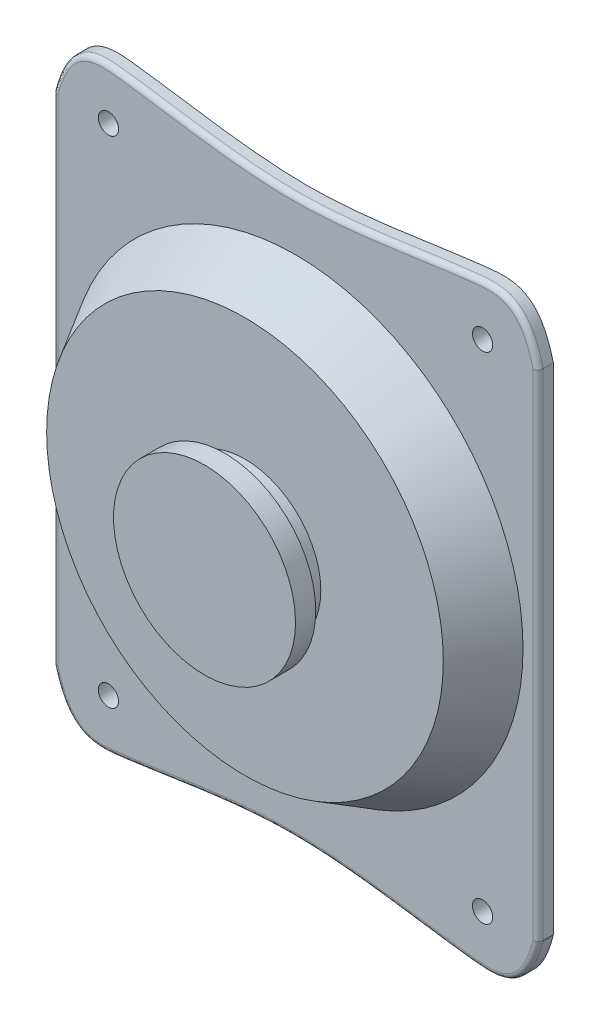
SolidWorks part; units mm, degrees
ref_plane "Front Plane" through (0, 0, 0) normal (0, 0, 1) x (1, 0, 0)
ref_plane "Top Plane" through (0, 0, 0) normal (0, 1, 0) x (1, 0, 0)
ref_plane "Right Plane" through (0, 0, 0) normal (1, 0, 0) x (0, 0, -1)
sketch "Sketch1" plane through (0, 0, 0) normal (0, 0, 1) x (1, 0, 0)
  line L2 (-24, 24.5) -> (-24, -24.5)
  line L4 (24, 24.5) -> (24, -24.5)
  line L5 (-24, 0) -> (24, 0) construction
  spline S0 degree 3 poles (-24, -24.5) (-22.6056, -29.9523) (-14.1064, -29.1494) (-0.2309, -26.3219) (15.046, -29.3894) (22.6642, -29.8454) (24, -24.5) knots 0 0 0 0 0.159887 0.492954 0.826022 1 1 1 1
  spline S1 degree 3 poles (-24, 24.5) (-22.6056, 29.9523) (-14.1064, 29.1494) (-0.2309, 26.3219) (15.046, 29.3894) (22.6642, 29.8454) (24, 24.5) knots 0 0 0 0 0.159887 0.492954 0.826022 1 1 1 1
  point P4 (-19, -29.4992)
  point P5 (19, -29.4992)
  point P6 (-24, -24.5)
  point P7 (24, -24.5)
  point P8 (0, -27.5)
extrude "Boss-Extrude1" add sketch "Sketch1" along normal blind 1.5
sketch "Sketch2" plane through (0, 0, 1.5) normal (0, 0, 1) x (1, 0, 0)
  circle A0 centre (0, 0) radius 22.5
extrude "Boss-Extrude4" add sketch "Sketch2" along normal blind 5 draft 30
sketch "Sketch3" plane through (0, 0, 6.5) normal (0, 0, 1) x (1, 0, 0)
  circle A0 centre (0, 0) radius 7.5
extrude "Boss-Extrude5" add sketch "Sketch3" along normal blind 2
sketch "Sketch4" plane through (0, 0, 8.5) normal (0, 0, 1) x (1, 0, 0)
  circle A0 centre (0, 0) radius 9
extrude "Boss-Extrude7" add sketch "Sketch4" along normal blind 2
fillet "Fillet4" radius 0.5 4 edges at (-24, 0, 1.5) (24, 0, 1.5)
sketch "Sketch5" plane through (0, 0, 1.5) normal (0, 0, 1) x (1, 0, 0)
  line L0 (23.5, -24.438) -> (23.5, 24.438) construction
  line L1 (0, 27) -> (0, -27) construction
  line L2 (-23.5, 0) -> (23.5, 0) construction
  line L3 (-23.5, 24.4366) -> (-23.5, -24.4366) construction
  circle A0 centre (18.5, -24.5) radius 1
  circle A1 centre (-18.5, -24.5) radius 1
  circle A2 centre (18.5, 24.5) radius 1
  circle A3 centre (-18.5, 24.5) radius 1
  spline S0 degree 3 poles (23.5, 24.438) (23.3649, 24.9705) (23.2056, 25.4945) (22.8028, 26.5126) (22.5583, 27.0108) (22.0826, 27.6811) (21.903, 27.8939) (21.5044, 28.2683) (21.2827, 28.4322) (20.7982, 28.6965) (20.543, 28.7933) (20.0115, 28.9289) (19.7368, 28.9672) (18.9221, 29.0217) (18.3788, 28.9835) (17.2921, 28.8747) (16.7499, 28.8076) (15.1245, 28.6027) (14.043, 28.4508) (10.7993, 27.9884) (8.637, 27.6712) (4.2973, 27.1834) (2.1216, 27.0105) (-2.2508, 26.9887) (-4.4207, 27.142) (-8.7434, 27.6174) (-10.8963, 27.9392) (-14.1261, 28.4176) (-15.2028, 28.5762) (-16.5506, 28.7599) (-16.8203, 28.7959) (-17.3599, 28.866) (-17.6299, 28.9007) (-18.1706, 28.9586) (-18.4412, 28.9819) (-18.9837, 29.0036) (-19.2568, 29.0021) (-19.7997, 28.9565) (-20.0668, 28.9127) (-20.5885, 28.7645) (-20.8441, 28.658) (-21.3097, 28.3875) (-21.5243, 28.2225) (-21.9177, 27.8423) (-22.0901, 27.6343) (-22.4012, 27.1929) (-22.5403, 26.9586) (-22.7907, 26.4761) (-22.9015, 26.2295) (-23.2031, 25.478) (-23.3636, 24.9618) (-23.5, 24.4366) knots 0 0 0 0 0.03125 0.03125 0.0625 0.0625 0.078125 0.078125 0.09375 0.09375 0.109375 0.109375 0.125 0.125 0.15625 0.15625 0.1875 0.1875 0.25 0.25 0.375 0.375 0.5 0.5 0.625 0.625 0.75 0.75 0.8125 0.8125 0.828125 0.828125 0.84375 0.84375 0.859375 0.859375 0.875 0.875 0.890625 0.890625 0.90625 0.90625 0.921875 0.921875 0.9375 0.9375 0.953125 0.953125 0.96875 0.96875 1 1 1 1 construction
  spline S1 degree 3 poles (-23.5, -24.4366) (-23.3635, -24.9622) (-23.2031, -25.4775) (-22.8033, -26.4746) (-22.5662, -26.9573) (-22.0929, -27.6312) (-21.9175, -27.8424) (-21.5256, -28.2213) (-21.3043, -28.3916) (-20.833, -28.6635) (-20.582, -28.7672) (-20.0521, -28.916) (-19.7817, -28.959) (-18.9686, -29.0244) (-18.4182, -28.9859) (-17.6038, -28.8976) (-17.3331, -28.8626) (-16.7917, -28.7921) (-15.4389, -28.6112) (-14.0885, -28.412) (-10.8478, -27.932) (-8.6874, -27.6096) (-4.3512, -27.136) (-2.1751, -26.9852) (2.2068, -27.015) (4.3805, -27.1911) (8.7129, -27.6816) (10.8715, -27.9989) (14.1108, -28.4604) (15.1908, -28.6117) (16.8134, -28.8153) (17.3543, -28.8824) (18.4393, -28.988) (18.9853, -29.0232) (19.7985, -28.9597) (20.071, -28.9176) (20.5941, -28.7755) (20.8478, -28.6742) (21.3237, -28.4041) (21.5387, -28.2401) (21.9303, -27.8636) (22.1059, -27.6513) (22.4159, -27.2081) (22.5525, -26.9749) (22.7998, -26.4918) (22.9103, -26.2419) (23.2086, -25.4844) (23.3662, -24.9653) (23.5, -24.438) knots 0 0 0 0 0.03125 0.03125 0.0625 0.0625 0.078125 0.078125 0.09375 0.09375 0.109375 0.109375 0.125 0.125 0.15625 0.15625 0.171875 0.171875 0.1875 0.25 0.25 0.375 0.375 0.5 0.5 0.625 0.625 0.75 0.75 0.8125 0.8125 0.84375 0.84375 0.875 0.875 0.890625 0.890625 0.90625 0.90625 0.921875 0.921875 0.9375 0.9375 0.953125 0.953125 0.96875 0.96875 1 1 1 1 construction
  dimension "D1" = 5
extrude "Cut-Extrude1" cut sketch "Sketch5" against normal blind 2
